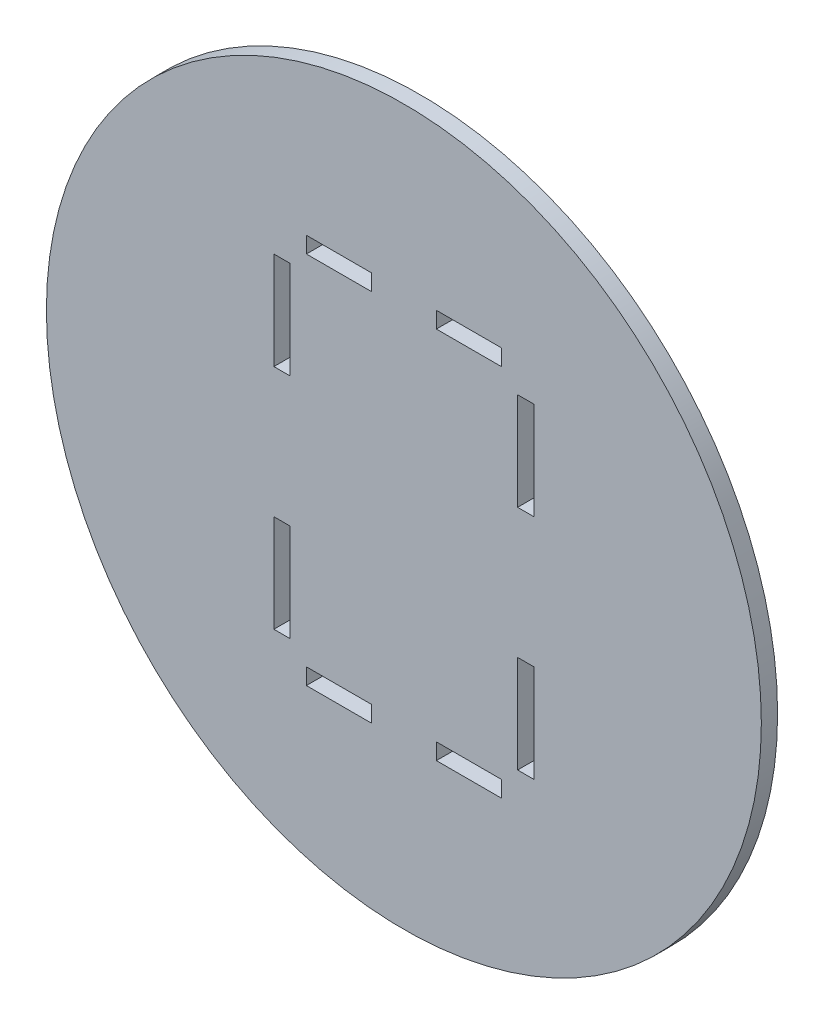
SolidWorks part; units mm, degrees
ref_plane "Front Plane" through (0, 0, 0) normal (0, 0, 1) x (1, 0, 0)
ref_plane "Top Plane" through (0, 0, 0) normal (0, 1, 0) x (1, 0, 0)
ref_plane "Right Plane" through (0, 0, 0) normal (1, 0, 0) x (0, 0, -1)
sketch "Sketch1" plane through (0, 0, 0) normal (0, 0, 1) x (1, 0, 0)
  line L0 (-40, 60) -> (40, 60) construction
  line L1 (40, 60) -> (40, -60) construction
  line L2 (40, -60) -> (-40, -60) construction
  line L3 (-40, -60) -> (-40, 60) construction
  line L5 (-30, 60) -> (-10, 60)
  line L6 (-30, 60) -> (-30, 55)
  line L7 (-30, 55) -> (-10, 55)
  line L8 (-10, 60) -> (-10, 55)
  line L9 (10, 60) -> (30, 60)
  line L10 (10, 60) -> (10, 55)
  line L11 (10, 55) -> (30, 55)
  line L12 (30, 60) -> (30, 55)
  line L13 (40, 50) -> (35, 50)
  line L14 (40, 50) -> (40, 20)
  line L15 (40, 20) -> (35, 20)
  line L16 (35, 50) -> (35, 20)
  line L17 (40, -20) -> (35, -20)
  line L18 (40, -20) -> (40, -50)
  line L19 (40, -50) -> (35, -50)
  line L20 (35, -20) -> (35, -50)
  line L21 (30, -60) -> (10, -60)
  line L22 (30, -60) -> (30, -55)
  line L23 (30, -55) -> (10, -55)
  line L24 (10, -60) -> (10, -55)
  line L25 (-10, -60) -> (-30, -60)
  line L26 (-10, -60) -> (-10, -55)
  line L27 (-10, -55) -> (-30, -55)
  line L28 (-30, -60) -> (-30, -55)
  line L29 (-40, -50) -> (-35, -50)
  line L30 (-40, -50) -> (-40, -20)
  line L31 (-40, -20) -> (-35, -20)
  line L32 (-35, -50) -> (-35, -20)
  line L33 (-40, 20) -> (-35, 20)
  line L34 (-40, 20) -> (-40, 50)
  line L35 (-40, 50) -> (-35, 50)
  line L36 (-35, 20) -> (-35, 50)
  circle A0 centre (0, 0) radius 110
  point P6 (0, -60)
  dimension "D1" = 220
  dimension "D2" = 80
  dimension "D3" = 120
  dimension "D4" = 40
  dimension "D5" = 60
  dimension "D6" = 10
  dimension "D7" = 20
  dimension "D8" = 20
  dimension "D9" = 20
  dimension "D10" = 10
  dimension "D11" = 30
  dimension "D12" = 40
  dimension "D13" = 30
  dimension "D14" = 10
  dimension "D15" = 20
  dimension "D16" = 20
  dimension "D17" = 20
  dimension "D18" = 10
  dimension "D19" = 30
  dimension "D20" = 40
  dimension "D21" = 30
  dimension "D22" = 5
  dimension "D23" = 5
  dimension "D24" = 5
  dimension "D25" = 5
  dimension "D26" = 5
  dimension "D27" = 5
  dimension "D28" = 5
  dimension "D29" = 5
extrude "Boss-Extrude1" add sketch "Sketch1" along normal blind 5
